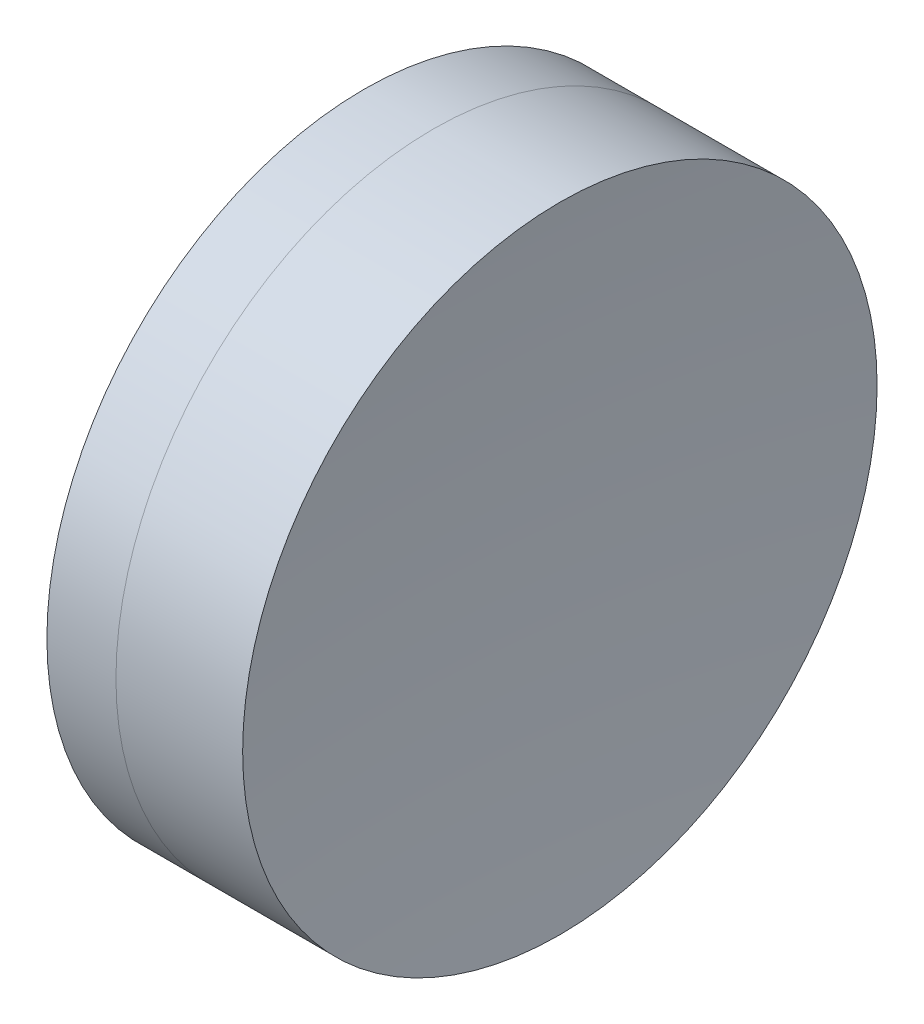
SolidWorks part; units mm, degrees
ref_plane "前视基准面" through (0, 0, 0) normal (0, 0, 1) x (1, 0, 0)
ref_plane "上视基准面" through (0, 0, 0) normal (0, 1, 0) x (1, 0, 0)
ref_plane "右视基准面" through (0, 0, 0) normal (1, 0, 0) x (0, 0, -1)
sketch "草图1" plane through (0, 0, 0) normal (0, 1, 0) x (1, 0, 0)
  line L0 (-0.8161, 0) -> (45.8933, 0) construction
  line L1 (37.2067, -6.35) -> (38.5887, -6.35)
  line L2 (37.2067, 6.35) -> (38.5887, 6.35)
  arc A0 (38.5887, -6.35) -> (38.5887, 6.35) centre (11.462, 0) ccw
  arc A1 (37.2067, 6.35) -> (37.2067, -6.35) centre (59.552, 0) ccw
  point P4 (45.8933, 0)
  point P10 (36.322, 0)
  point P11 (39.322, 0)
  dimension "D3" = 23.23
  dimension "D4" = 27.86
  dimension "D1" = 6.35
  dimension "D2" = 6.35
  dimension "D5" = 3
revolve "旋转1" add sketch "草图1" angle 360 about L0
sketch "草图2" plane through (0, 0, 0) normal (0, 1, 0) x (1, 0, 0)
  line L0 (-0.5519, 0) -> (45.4982, 0) construction
  line L2 (38.5887, 6.35) -> (41.125, 6.35)
  line L3 (38.5887, -6.35) -> (41.125, -6.35)
  arc A0 (41.125, 6.35) -> (41.125, -6.35) centre (107.502, 0) ccw
  arc A1 (38.5887, -6.35) -> (38.5887, 6.35) centre (11.462, 0) ccw construction
  arc A2 (38.5887, -6.35) -> (38.5887, 6.35) centre (11.462, 0) ccw
  point P4 (39.322, 0)
  point P8 (40.822, 0)
  point P9 (45.4982, 0)
  dimension "D1" = 66.68
  dimension "D2" = 1.5
revolve "旋转2" add sketch "草图2" angle 360 about L0
